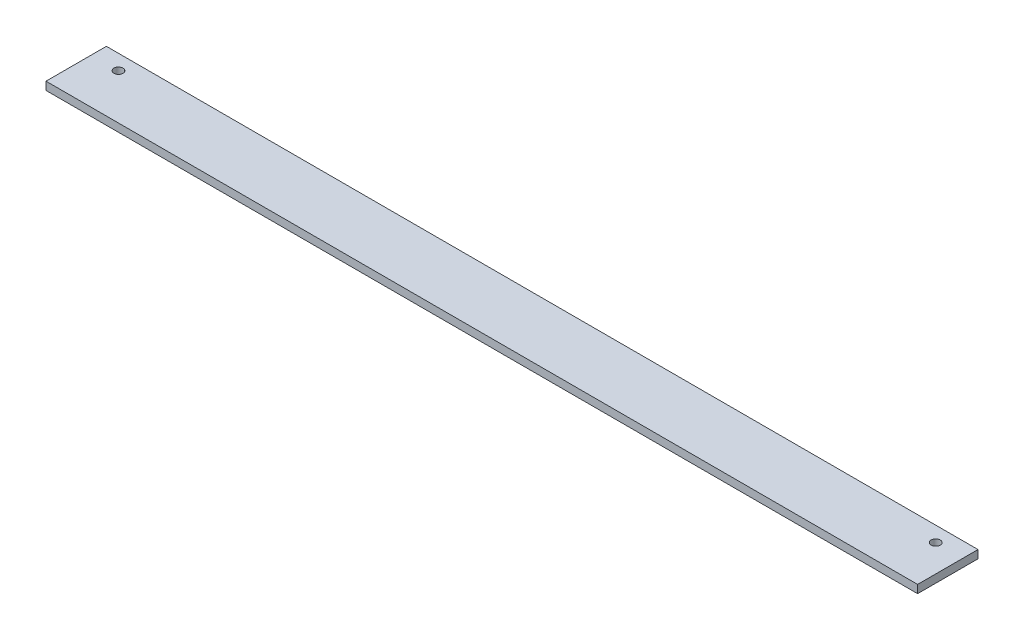
SolidWorks part; units mm, degrees
ref_plane "Спереди" through (0, 0, 0) normal (0, 0, 1) x (1, 0, 0)
ref_plane "Сверху" through (0, 0, 0) normal (0, 1, 0) x (1, 0, 0)
ref_plane "Справа" through (0, 0, 0) normal (1, 0, 0) x (0, 0, -1)
sketch "Эскиз1" plane through (0, 0, 0) normal (1, 0, 0) x (0, 0, -1)
  line L1 (-15, -2) -> (15, -2)
  line L2 (-15, -2) -> (-15, 2)
  line L3 (-15, 2) -> (15, 2)
  line L4 (15, -2) -> (15, 2)
  line L5 (-15, -2) -> (15, 2) construction
  line L6 (-15, 2) -> (15, -2) construction
  point P0 (0, 0)
  dimension "D1" = 4
  dimension "D2" = 30
extrude "Бобышка-Вытянуть1" add sketch "Эскиз1" along normal blind 433
sketch "Эскиз2" plane through (0, 2, 0) normal (0, 1, 0) x (1, 0, 0)
  line L0 (433, 15) -> (0, 15) construction
  line L1 (0, 15) -> (0, -15) construction
  line L2 (433, 15) -> (433, -15) construction
  circle A0 centre (13.5, 7.5) radius 2.25
  circle A1 centre (419.5, 7.5) radius 2.25
  dimension "D1" = 4.5
  dimension "D4" = 4.5
  dimension "D2" = 7.5
  dimension "D3" = 13.5
  dimension "D5" = 13.5
  dimension "D6" = 7.5
extrude "Вырез-Вытянуть1" cut sketch "Эскиз2" against normal through all
